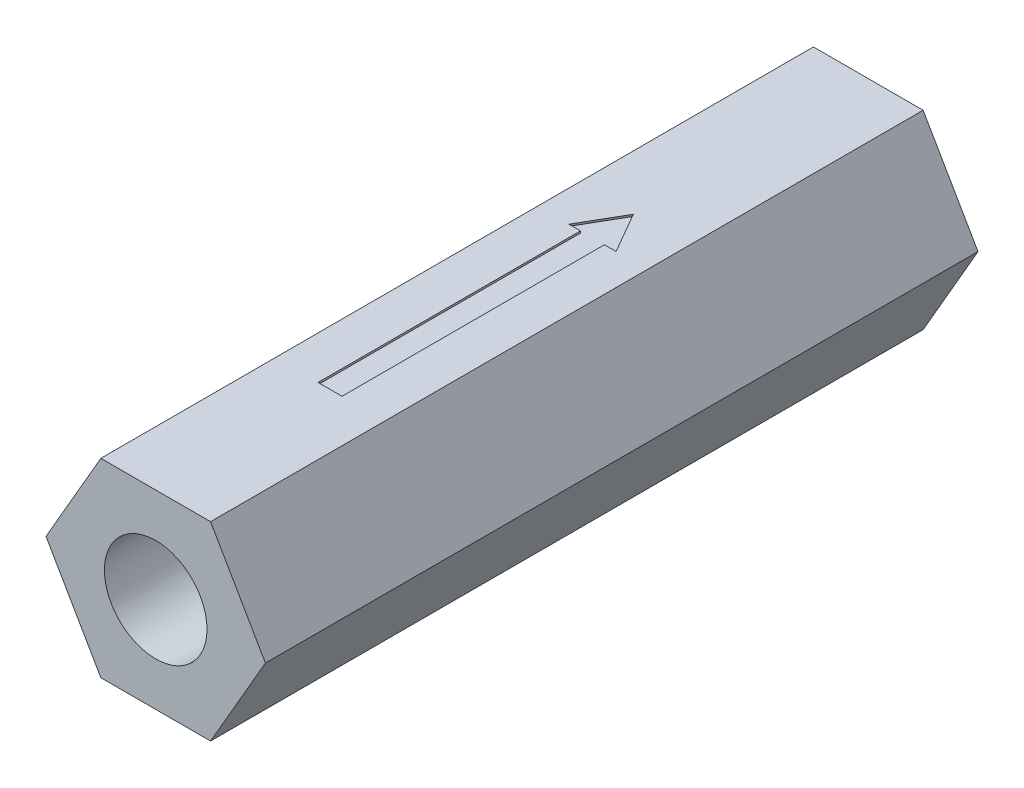
SolidWorks part; units mm, degrees
material "Brass"
ref_plane "Front Plane" through (0, 0, 0) normal (0, 0, 1) x (1, 0, 0)
ref_plane "Top Plane" through (0, 0, 0) normal (0, 1, 0) x (1, 0, 0)
ref_plane "Right Plane" through (0, 0, 0) normal (1, 0, 0) x (0, 0, -1)
sketch "Sketch1" plane through (0, 0, 0) normal (0, 0, 1) x (1, 0, 0)
  line L1 (14.6647, 0) -> (7.3323, 12.7)
  line L2 (7.3323, 12.7) -> (-7.3323, 12.7)
  line L3 (-7.3323, 12.7) -> (-14.6647, 0)
  line L4 (-14.6647, 0) -> (-7.3323, -12.7)
  line L5 (-7.3323, -12.7) -> (7.3323, -12.7)
  line L6 (7.3323, -12.7) -> (14.6647, 0)
  circle A0 centre (0, 0) radius 12.7 construction
  dimension "D1" = 25.4
  dimension "D2" = 7.3323
extrude "Boss-Extrude1" add sketch "Sketch1" along normal blind 95.25
sketch "Sketch2" plane through (0, 0, 95.25) normal (0, 0, 1) x (1, 0, 0)
  circle A0 centre (0, 0) radius 6.858
  dimension "D1" = 13.716
extrude "Cut-Extrude1" cut sketch "Sketch2" against normal blind 17.145
sketch "Sketch3" plane through (0, 0, 0) normal (0, 0, -1) x (-1, 0, 0)
  circle A0 centre (0, 0) radius 6.858
  dimension "D1" = 13.716
extrude "Cut-Extrude2" cut sketch "Sketch3" against normal blind 17.145
sketch "Sketch4" plane through (0, 12.7, 0) normal (0, 1, 0) x (1, 0, 0)
  line L0 (0, -95.25) -> (0, 0) construction
  line L1 (7.3323, -95.25) -> (-7.3323, -95.25) construction
  line L2 (7.3323, 0) -> (-7.3323, 0) construction
sketch "Sketch5" plane through (0, 12.7, 0) normal (0, 1, 0) x (1, 0, 0)
  line L1 (-1.6005, -71.9491) -> (1.6005, -71.9491)
  line L2 (-1.6005, -71.9491) -> (-1.6005, -42.1963)
  line L4 (1.6005, -71.9491) -> (1.6005, -36.8666)
  line L6 (-1.6005, -42.1963) -> (-1.6005, -36.8666)
  line L7 (0, -31.4049) -> (-3.1533, -36.8666)
  line L8 (-3.1533, -36.8666) -> (-1.6005, -36.8666)
  line L9 (3.1533, -36.8666) -> (0, -31.4049)
  line L10 (1.6005, -36.8666) -> (3.1533, -36.8666)
  point P0 (0, -53.4975)
extrude "Cut-Extrude3" cut sketch "Sketch5" against normal blind 0.254
